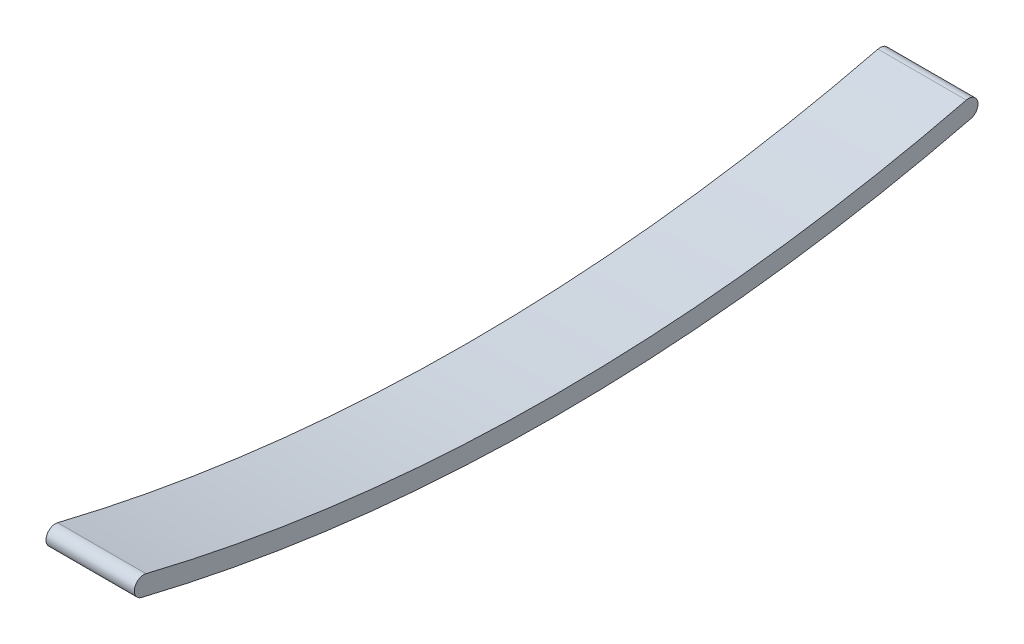
SolidWorks part; units mm, degrees
ref_plane "Front Plane" through (0, 0, 0) normal (0, 0, 1) x (1, 0, 0)
ref_plane "Top Plane" through (0, 0, 0) normal (0, 1, 0) x (1, 0, 0)
ref_plane "Right Plane" through (0, 0, 0) normal (1, 0, 0) x (0, 0, -1)
sketch "Sketch1" plane through (0, 0, 0) normal (1, 0, 0) x (0, 0, -1)
  line L0 (-37.5, 0) -> (37.5, 0) construction
  line L1 (0, 12.714) -> (0, -21.3049) construction
  line L2 (32.5, 12.714) -> (32.5, -21.3049) construction
  line L3 (-32.5, 12.714) -> (-32.5, -21.3049) construction
  arc A4 (-32.5, -4.0761) -> (32.5, -4.0761) centre (0, 128.5536) ccw
  arc A6 (-32.857, -5.533) -> (32.857, -5.533) centre (0, 128.5536) ccw
  arc A7 (-32.5, -4.0761) -> (-32.857, -5.533) centre (-32.6785, -4.8045) ccw
  arc A8 (32.5, -4.0761) -> (32.857, -5.533) centre (32.6785, -4.8045) cw
  point P5 (-37.5, 0)
  point P6 (40.25, 0)
  point P7 (37.5, 0)
  point P9 (-37.5, -2.75)
  point P11 (37.5, -2.75)
  point P13 (0, 128.5536)
  point P14 (-37.0881, -1.3077)
  point P15 (37.0881, -1.3077)
  point P18 (-34.75, 0)
  point P26 (0, 0)
  point P27 (0, 0)
  dimension "D3" = 1.5
  dimension "D8" = 65
  dimension "D1" = 75
  dimension "D2" = 37.5
  dimension "D9" = 32.5
extrude "Boss-Extrude1" add sketch "Sketch1" along normal blind 7
